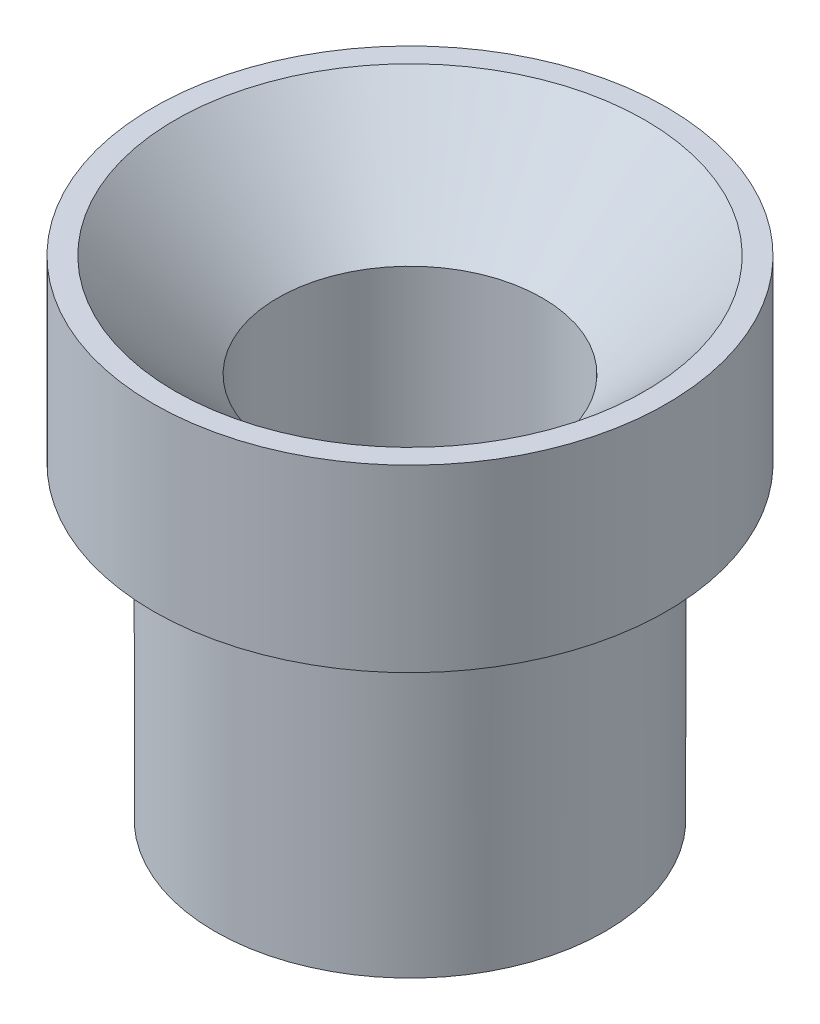
SolidWorks part; units mm, degrees
material "Nickel"
ref_plane "Front Plane" through (0, 0, 0) normal (0, 0, 1) x (1, 0, 0)
ref_plane "Top Plane" through (0, 0, 0) normal (0, 1, 0) x (1, 0, 0)
ref_plane "Right Plane" through (0, 0, 0) normal (1, 0, 0) x (0, 0, -1)
sketch "Sketch1" plane through (0, 0, 0) normal (0, 1, 0) x (1, 0, 0)
  circle A0 centre (0, 0) radius 5
  dimension "D1" = 10
extrude "Boss-Extrude1" add sketch "Sketch1" along normal blind 3.5
sketch "Sketch2" plane through (0, 3.5, 0) normal (0, 1, 0) x (1, 0, 0)
  circle A0 centre (0, 0) radius 2.575
  dimension "D1" = 5.15
extrude "Cut-Extrude1" cut sketch "Sketch2" against normal blind 3.5
chamfer "Chamfer1" distance 2 angle 45 1 edges at (0, 3.5, 2.575)
sketch "Sketch3" plane through (0, 0, 0) normal (0, -1, 0) x (1, 0, 0)
  circle A0 centre (0, 0) radius 3.8
  dimension "D1" = 7.6
extrude "Boss-Extrude2" add sketch "Sketch3" along normal blind 6
sketch "Sketch4" plane through (0, -6, 0) normal (0, -1, 0) x (1, 0, 0)
  circle A0 centre (0, 0) radius 2.575
extrude "Cut-Extrude2" cut sketch "Sketch4" against normal blind 6
